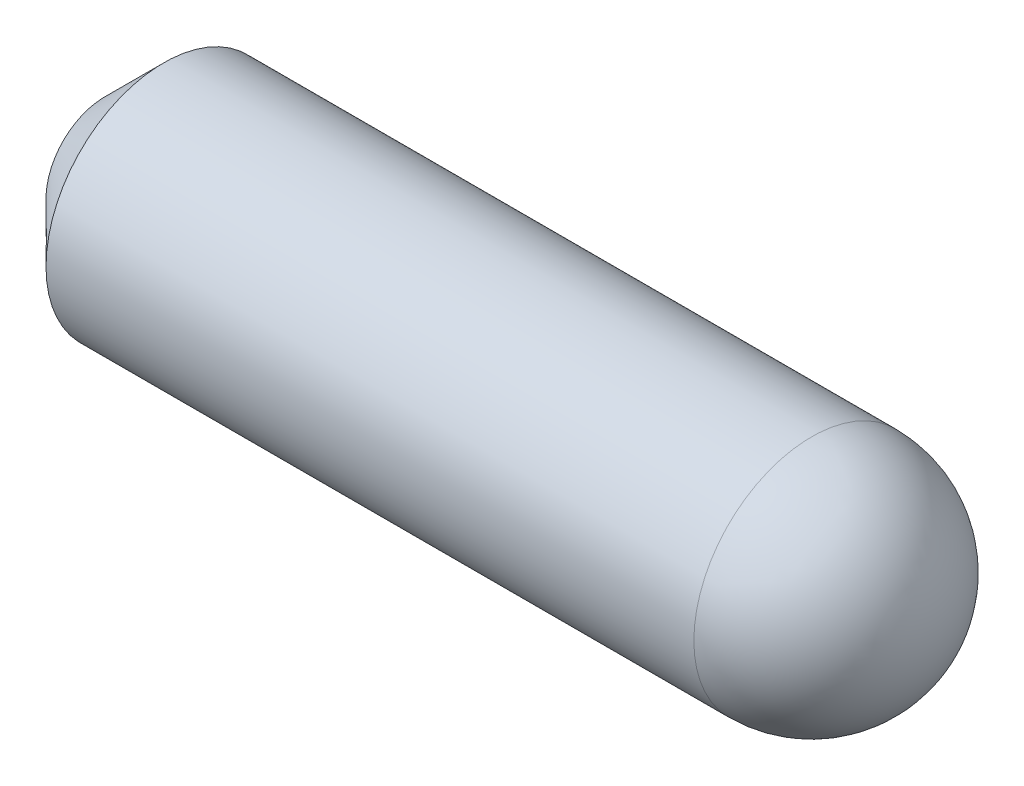
SolidWorks part; units mm, degrees
ref_plane "Front" through (0, 0, 0) normal (0, 0, 1) x (1, 0, 0)
ref_plane "Top" through (0, 0, 0) normal (0, 1, 0) x (1, 0, 0)
ref_plane "Right" through (0, 0, 0) normal (1, 0, 0) x (0, 0, -1)
sketch "Sketch1" plane through (0, 0, 0) normal (0, 0, 1) x (1, 0, 0)
  line L0 (-4.8015, 0) -> (25.8023, 0) construction
  line L2 (0, 0) -> (14, 0)
  line L3 (0, 0) -> (0, 2)
  line L4 (0, 2) -> (14, 2)
  line L5 (14, 0) -> (14, 2)
  dimension "D1" = 14
  dimension "D2" = 4
revolve "Revolve1" add sketch "Sketch1" angle 360 about L0
chamfer "Chamfer1" distance 1 angle 45 1 edges at (0, 0, 2)
fillet "Fillet1" radius 2 1 edges at (14, 0, 2)
